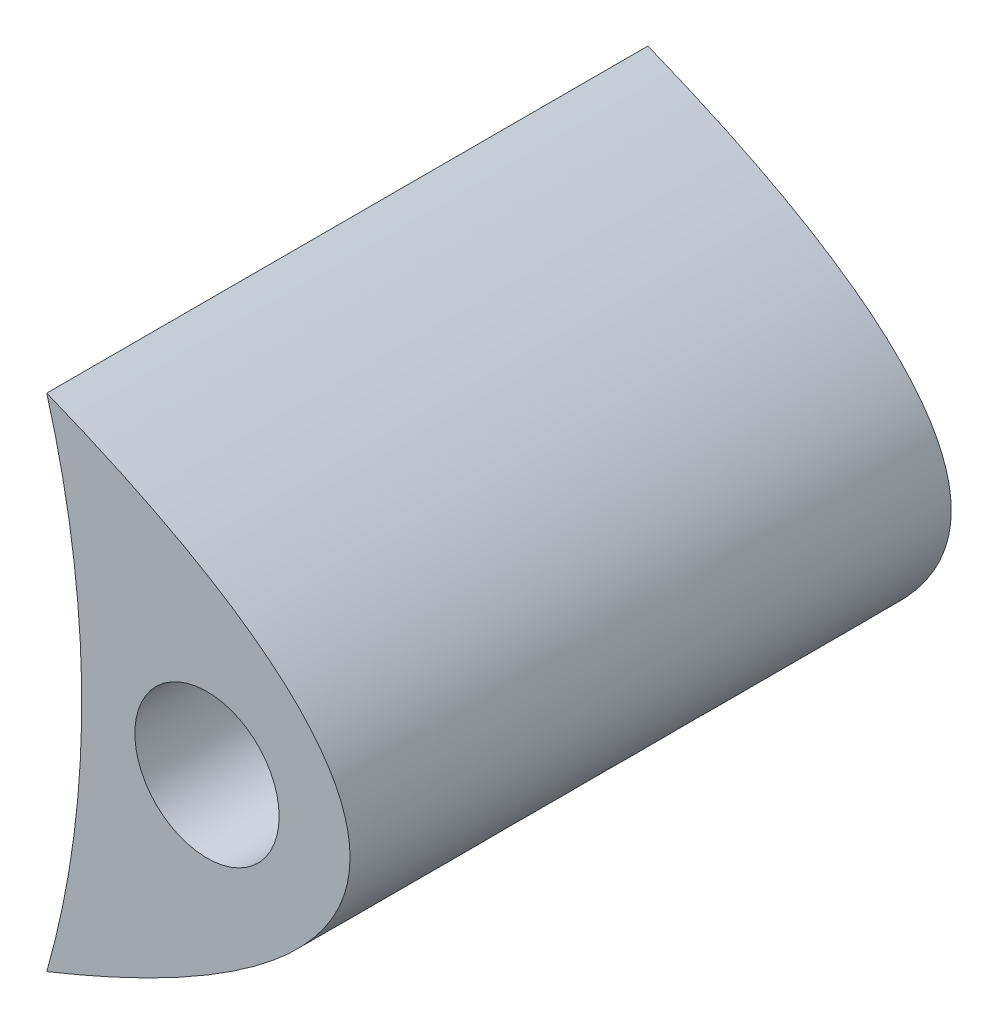
SolidWorks part; units mm, degrees
material "Ceramic Porcelain"
ref_plane "Front Plane" through (0, 0, 0) normal (0, 0, 1) x (1, 0, 0)
ref_plane "Top Plane" through (0, 0, 0) normal (0, 1, 0) x (1, 0, 0)
ref_plane "Right Plane" through (0, 0, 0) normal (1, 0, 0) x (0, 0, -1)
sketch "Sketch2" plane through (0, 0, 0) normal (0, 1, 0) x (1, 0, 0)
  line L0 (0, 0) -> (0, -15.24) construction
  dimension "D1" = 15.24
sketch "Sketch1" plane through (0, 0, 0) normal (0, 0, 1) x (1, 0, 0)
  line L4 (-4.0618, 6.35) -> (-8.0431, 20.3267) construction
  line L11 (0, 0) -> (0, 20.3158) construction
  line L13 (-3.627, 0) -> (3.627, 0) construction
  line L16 (-4.0618, 6.35) -> (-34.0424, 6.35) construction
  line L17 (-26.3536, 0) -> (3.627, 0) construction
  arc A3 (5.3056, 6.35) -> (5.3056, -6.35) centre (-16.9862, 0) cw construction
  arc A4 (-4.0618, 6.35) -> (-4.0618, -6.35) centre (-26.3536, 0) cw
  ellipse E0 centre (-132.6952, 0) end of major axis (3.627, 0) minor radius 19.1789 (-4.0618, 6.35) -> (-4.0618, -6.35) cw
  point P0 (0, 0)
  point P5 (-3.175, 0)
  point P27 (6.1924, 0)
  dimension "D1" = 15.9
  dimension "D5" = 12.7
  dimension "D4" = 2.5654
  dimension "D2" = 3.175
  dimension "D3" = 9.3674
extrude "Boss-Extrude1" add sketch "Sketch1" against normal up to vertex (15.24 mm away)
hole_wizard "#6 Clearance Hole2" positions "3DSketch1" profile "Sketch3" hole size "#6" standard "ANSI Inch" end condition up to next
sketch3d "3DSketch1"
  point P0 (0, 0, 0)
  point P3 (0, 0, 0)
sketch "Sketch3" plane through (0, 0, 0) normal (1, 0, 0) x (0, -1, 0)
  line L0 (0, 0) -> (0, 15.241)
  line L1 (0, 15.241) -> (1.8288, 15.241)
  line L2 (1.8288, 15.241) -> (1.8288, 0)
  line L5 (1.8288, 0) -> (0, 0)
  line L11 (0, -6.35) -> (0, 107.95) construction
  dimension "Thru Hole Dia." = 3.6576
  dimension "Thru Hole Depth" = 15.241
equation "\"D1@Sketch2\"=\"rotor tip@[TP] [Turb] Turbine.Assembly\"-\"rotor base@[TP] [Turb] Turbine.Assembly\""
equation "\"D1@Sketch1\"=\"blade angle@[TP] [Turb] Turbine.Assembly\""
equation "\"D5@Sketch1\"=\"blade width@[TP] [Turb] Turbine.Assembly\""
equation "\"D4@Sketch1\"=\"blade opening@[TP] [Turb] Turbine.Assembly\""
equation "\"D3@Sketch1\"=2*pi*\"rotor pitchline@[TP] [Turb] Turbine.Assembly\"/\"blade number@[TP] [Turb] Turbine.Assembly\""
